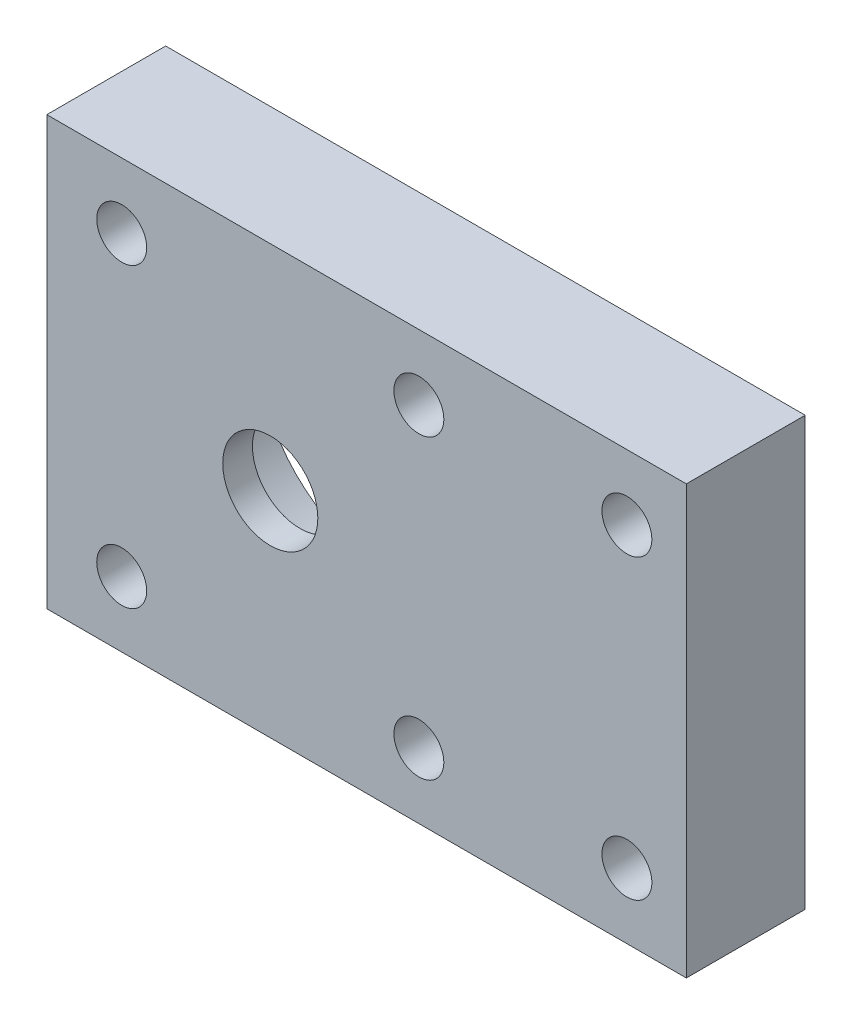
SolidWorks part; units mm, degrees
ref_plane "Front Plane" through (0, 0, 0) normal (0, 0, 1) x (1, 0, 0)
ref_plane "Top Plane" through (0, 0, 0) normal (0, 1, 0) x (1, 0, 0)
ref_plane "Right Plane" through (0, 0, 0) normal (1, 0, 0) x (0, 0, -1)
sketch "Sketch1" plane through (0, 0, 0) normal (0, 0, 1) x (1, 0, 0)
  line L0 (-22.5, 32.5) -> (-35, 20) construction
  line L1 (0, 0) -> (-53.8, 0)
  line L2 (0, 0) -> (0, 40)
  line L3 (0, 40) -> (-53.8, 40)
  line L4 (-53.8, 0) -> (-53.8, 40)
  line L5 (-35, 20) -> (-40.5, 25.5) construction
  line L6 (-10, 20) -> (-17.5441, 20) construction
  circle A0 centre (-35, 20) radius 11 construction
  circle A1 centre (-10, 20) radius 4 construction
  circle A2 centre (-22.5, 32.5) radius 2.1
  circle A3 centre (-47.5, 7.5) radius 2.1
  circle A4 centre (-47.5, 32.5) radius 2.1
  circle A5 centre (-22.5, 7.5) radius 2.1
  circle A6 centre (-5, 32.5) radius 2.1
  circle A7 centre (-5, 7.5) radius 2.1
  circle A8 centre (-35, 20) radius 4
  dimension "D3" = 35
  dimension "D4" = 20
  dimension "D5" = 22
  dimension "D6" = 8
  dimension "D7" = 25
  dimension "D8" = 4.2
  dimension "D9" = 12.5
  dimension "D10" = 12.5
  dimension "D11" = 4.2
  dimension "D12" = 4.2
  dimension "D13" = 12.5
  dimension "D14" = 12.5
  dimension "D15" = 12.5
  dimension "D16" = 12.5
  dimension "D17" = 4.2
  dimension "D18" = 5
  dimension "D19" = 7.5
  dimension "D20" = 8
  dimension "D1" = 53.8
  dimension "D2" = 40
extrude "Boss-Extrude1" add sketch "Sketch1" along normal blind 10
sketch "Sketch2" plane through (0, 0, 0) normal (0, 0, -1) x (-1, 0, 0)
  circle A0 centre (35, 20) radius 11
  dimension "D1" = 22
extrude "Cut-Extrude1" cut sketch "Sketch2" against normal blind 7.5
sketch "Sketch3" plane through (0, 0, 0) normal (0, -1, 0) x (1, 0, 0)
  line L4 (-53.8, 0) -> (0, 0)
  line L5 (0, 0) -> (0, 10)
  line L6 (0, 10) -> (-53.8, 10)
  line L7 (-53.8, 10) -> (-53.8, 0)
  line L8 (-53.8, 0) -> (0, 0)
  line L9 (0, 0) -> (0, 10)
  line L10 (0, 10) -> (-53.8, 10)
  line L11 (-53.8, 10) -> (-53.8, 0)
  dimension "D1" = 0
extrude "Cut-Extrude2" cut sketch "Sketch3" against normal blind 2
sketch "Sketch4" plane through (0, 40, 0) normal (0, 1, 0) x (1, 0, 0)
  line L4 (0, 0) -> (-53.8, 0)
  line L5 (-53.8, 0) -> (-53.8, -10)
  line L6 (-53.8, -10) -> (0, -10)
  line L7 (0, -10) -> (0, 0)
  line L8 (0, 0) -> (-53.8, 0)
  line L9 (-53.8, 0) -> (-53.8, -10)
  line L10 (-53.8, -10) -> (0, -10)
  line L11 (0, -10) -> (0, 0)
  dimension "D1" = 0
extrude "Cut-Extrude3" cut sketch "Sketch4" against normal blind 2
